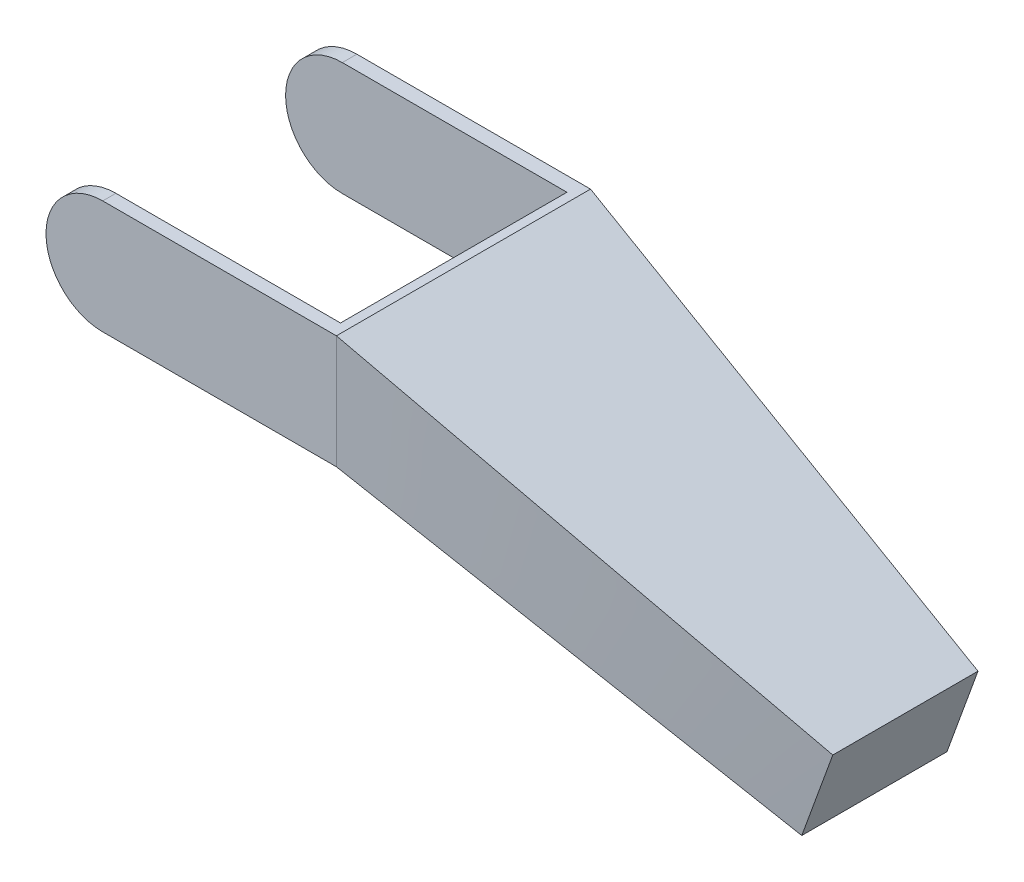
SolidWorks part; units mm, degrees
material "Окись алюминия"
ref_plane "Спереди" through (0, 0, 0) normal (0, 0, 1) x (1, 0, 0)
ref_plane "Сверху" through (0, 0, 0) normal (0, 1, 0) x (1, 0, 0)
ref_plane "Справа" through (0, 0, 0) normal (1, 0, 0) x (0, 0, -1)
other "Configuration Table"
sketch "Эскиз1" plane through (0, 0, 0) normal (0, 0, 1) x (1, 0, 0)
  line L0 (0, 12.5) -> (51.5, 12.5)
  line L1 (51.5, 12.5) -> (51.5, -12.5)
  line L2 (51.5, -12.5) -> (0, -12.5)
  arc A1 (0, 12.5) -> (0, -12.5) centre (0, 0) ccw
  dimension "D1" = 25
  dimension "D2" = 51.5
extrude "Бобышка-Вытянуть1" add sketch "Эскиз1" along normal mid plane 56
sketch "Эскиз2" plane through (0, 0, 0) normal (0, 0, 1) x (1, 0, 0)
  line L0 (0, 12.5) -> (49.5, 12.5)
  line L1 (51.5, 12.5) -> (0, 12.5) construction
  line L2 (49.5, 12.5) -> (49.5, -12.5)
  line L3 (0, -12.5) -> (51.5, -12.5) construction
  line L4 (49.5, -12.5) -> (0, -12.5)
  line L5 (51.5, -12.5) -> (51.5, 12.5) construction
  arc A0 (0, 12.5) -> (0, -12.5) centre (0, 0) ccw construction
  arc A1 (0, 12.5) -> (0, -12.5) centre (0, 0) ccw
  dimension "D1" = 2
extrude "Вырез-Вытянуть1" cut sketch "Эскиз2" against normal blind 24.8 and the other way blind 25.1 contours A1 L4 L2 L0
sketch "Эскиз3" plane through (51.5, 0, 0) normal (1, 0, 0) x (0, 0, -1)
  line L4 (28, -12.5) -> (28, 12.5)
  line L5 (28, 12.5) -> (-28, 12.5)
  line L6 (-28, 12.5) -> (-28, -12.5)
  line L7 (-28, -12.5) -> (28, -12.5)
  line L8 (28, -12.5) -> (28, 12.5)
  line L9 (28, 12.5) -> (-28, 12.5)
  line L10 (-28, 12.5) -> (-28, -12.5)
  line L11 (-28, -12.5) -> (28, -12.5)
  dimension "D1" = 0
sketch "Эскиз5" plane through (0, 0, 0) normal (0, 0, 1) x (1, 0, 0)
  line L0 (51.5, 0) -> (145.4693, -34.202) construction
  line L1 (51.5, 12.5) -> (51.5, -12.5) construction
  line L2 (51.5, 0) -> (89.4837, 0) construction
  line L3 (0, 0) -> (145.4693, -34.202) construction
  point P8 (145.4693, -34.202)
  dimension "D1" = 100
  dimension "D2" = 20
ref_plane "Плоскость1" through (145.4693, -34.202, 0) normal (0.9397, -0.342, 0) x (0, 0, -1)
sketch "Эскиз6" plane through (145.4693, -34.202, 0) normal (0.9397, -0.342, 0) x (0, 0, -1)
  line L0 (0, -68404.0287) -> (0, 68417.0198) construction
  line L1 (-16, 10) -> (16, 10)
  line L2 (-16, 10) -> (-16, -10)
  line L3 (-16, -10) -> (16, -10)
  line L4 (16, 10) -> (16, -10)
  line L5 (-16, 10) -> (16, -10) construction
  line L6 (-16, -10) -> (16, 10) construction
  point P0 (0, 0)
  dimension "D1" = 32
  dimension "D2" = 20
loft "По сечениям1" add profiles "Эскиз3", "Эскиз6"
